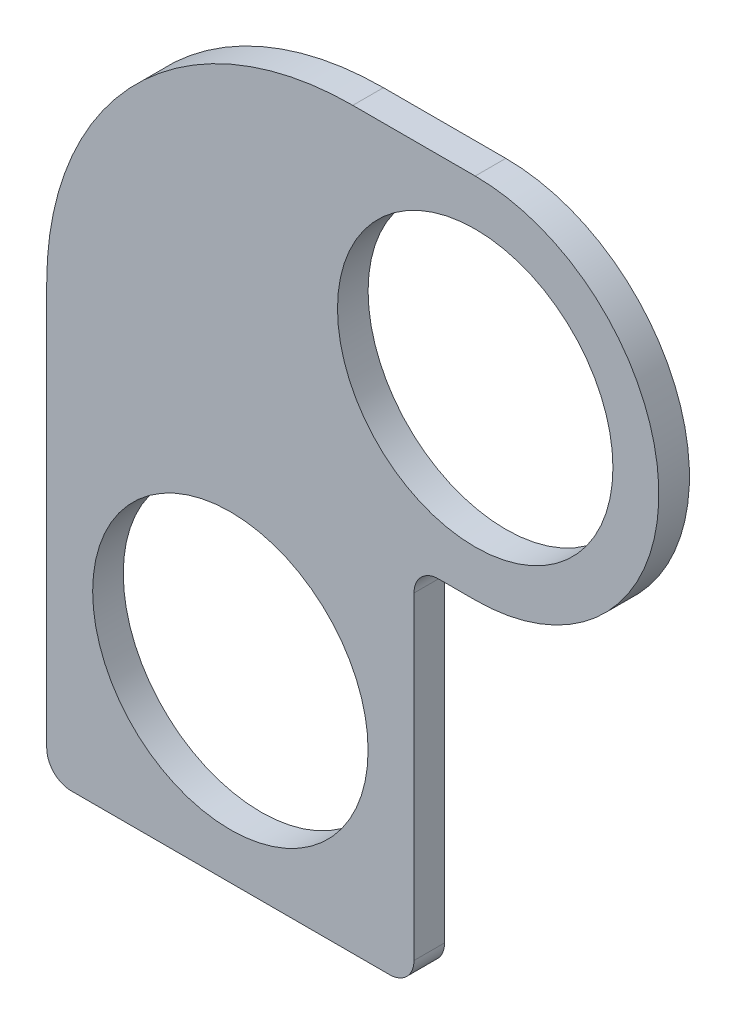
SolidWorks part; units mm, degrees
material "1060 Alloy"
ref_plane "Front Plane" through (0, 0, 0) normal (0, 0, 1) x (1, 0, 0)
ref_plane "Top Plane" through (0, 0, 0) normal (0, 1, 0) x (1, 0, 0)
ref_plane "Right Plane" through (0, 0, 0) normal (1, 0, 0) x (0, 0, -1)
sketch "Sketch1" plane through (0, 0, 0) normal (0, 0, 1) x (1, 0, 0)
  line L0 (25.4, 0) -> (-50.8, 0) construction
  line L1 (25.4, -19.05) -> (19.05, -19.05)
  line L4 (19.05, -19.05) -> (19.05, -57.15)
  line L5 (19.05, -57.15) -> (-19.05, -57.15)
  line L6 (-19.05, -57.15) -> (-19.05, -19.05)
  line L7 (-19.05, -19.05) -> (-19.05, -12.7)
  line L8 (12.7, 19.05) -> (25.4, 19.05)
  circle A1 centre (25.4, 0) radius 14.2875
  arc A3 (25.4, -19.05) -> (25.4, 19.05) centre (25.4, 0) ccw
  circle A4 centre (0, -38.1) radius 14.2875
  arc A5 (-19.05, -12.7) -> (12.7, 19.05) centre (12.7, -12.7) cw
  point P5 (6.35, 0)
  dimension "D1" = 38.1
  dimension "D2" = 28.575
  dimension "D4" = 19.05
  dimension "D5" = 28.575
  dimension "D8" = 31.75
  dimension "D3" = 25.4
  dimension "D6" = 38.1
  dimension "0.75" = 19.05
  dimension "D7" = 38.1
extrude "Boss-Extrude1" add sketch "Sketch1" along normal blind 3.175
fillet "Fillet1" radius 2.54 3 edges at (-19.05, -57.15, 1.5875) (19.05, -57.15, 1.5875) (19.05, -19.05, 1.5875)
